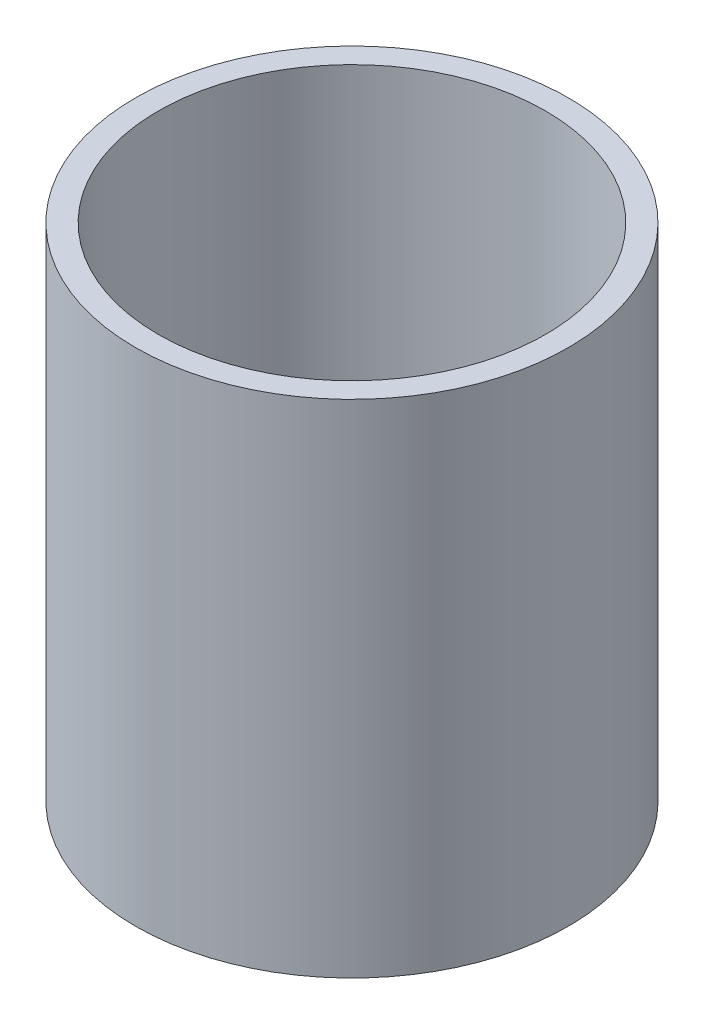
SolidWorks part; units mm, degrees
ref_plane "Front Plane" through (0, 0, 0) normal (0, 0, 1) x (1, 0, 0)
ref_plane "Top Plane" through (0, 0, 0) normal (0, 1, 0) x (1, 0, 0)
ref_plane "Right Plane" through (0, 0, 0) normal (1, 0, 0) x (0, 0, -1)
sketch "Sketch1" plane through (0, 0, 0) normal (0, 1, 0) x (1, 0, 0)
  circle A0 centre (0, 0) radius 17
  circle A1 centre (0, 0) radius 19
extrude "Boss-Extrude1" add sketch "Sketch1" along normal blind 44
